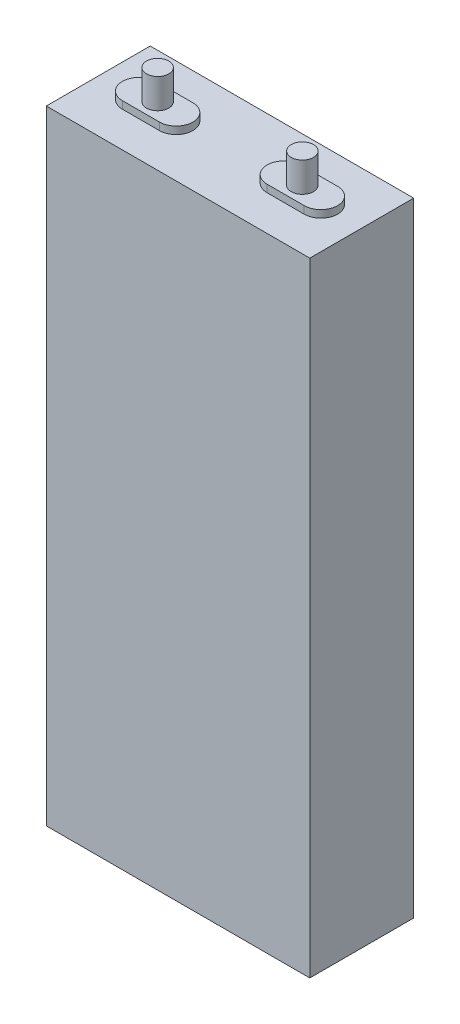
SolidWorks part; units mm, degrees
ref_plane "Plan de face" through (0, 0, 0) normal (0, 0, 1) x (1, 0, 0)
ref_plane "Plan de dessus" through (0, 0, 0) normal (0, 1, 0) x (1, 0, 0)
ref_plane "Plan de droite" through (0, 0, 0) normal (1, 0, 0) x (0, 0, -1)
sketch "Esquisse1" plane through (0, 0, 0) normal (0, 1, 0) x (1, 0, 0)
  line L0 (0, 21.531) -> (0, -24.0414) construction
  line L1 (-56.1931, 0) -> (70.6759, 0) construction
  line L3 (-35.5, 14) -> (35.5, 14)
  line L4 (-35.5, 14) -> (-35.5, -14)
  line L5 (-35.5, -14) -> (35.5, -14)
  line L6 (35.5, 14) -> (35.5, -14)
  dimension "D1" = 28
  dimension "D2" = 71
extrude "Boss.-Extru.1" add sketch "Esquisse1" along normal blind 168
sketch "Esquisse2" plane through (0, 168, 0) normal (0, 1, 0) x (1, 0, 0)
  line L0 (-39.2481, 0) -> (44.723, 0) construction
  line L1 (-24.5, 0) -> (-14.5, 0) construction
  line L2 (-24.5, 4.5) -> (-14.5, 4.5)
  line L3 (-24.5, -4.5) -> (-14.5, -4.5)
  line L4 (0, -17.1711) -> (0, 24.2101) construction
  line L5 (24.5, 0) -> (14.5, 0) construction
  line L6 (24.5, 4.5) -> (14.5, 4.5)
  line L7 (24.5, -4.5) -> (14.5, -4.5)
  arc A0 (-24.5, 4.5) -> (-24.5, -4.5) centre (-24.5, 0) ccw
  arc A1 (-14.5, -4.5) -> (-14.5, 4.5) centre (-14.5, 0) ccw
  arc A2 (24.5, 4.5) -> (24.5, -4.5) centre (24.5, 0) cw
  arc A3 (14.5, -4.5) -> (14.5, 4.5) centre (14.5, 0) cw
  point P5 (-19.5, 0)
  point P14 (19.5, 0)
  dimension "D2" = 4.5
  dimension "D1" = 19.5
  dimension "D3" = 10
extrude "Boss.-Extru.2" add sketch "Esquisse2" along normal blind 2
sketch "Esquisse3" plane through (0, 170, 0) normal (0, 1, 0) x (1, 0, 0)
  line L0 (-19.5, 8.5802) -> (-19.5, -8.9471) construction
  line L1 (-39.2189, 0) -> (40.2735, 0) construction
  line L2 (0, 11.1178) -> (0, -11.7207) construction
  circle A0 centre (-19.5, 0) radius 3
  circle A1 centre (19.5, 0) radius 3
  dimension "D1" = 6
extrude "Boss.-Extru.3" add sketch "Esquisse3" along normal blind 8
